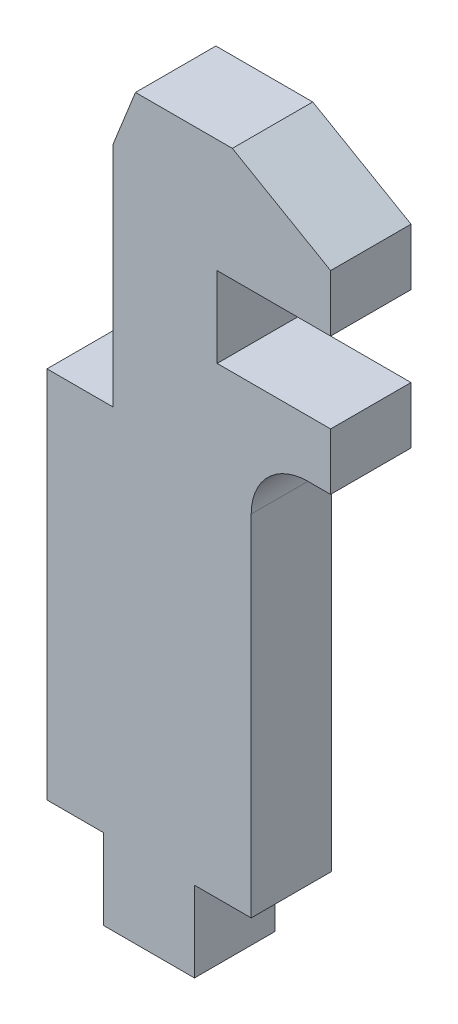
SolidWorks part; units mm, degrees
material "ABS PC"
ref_plane "Front Plane" through (0, 0, 0) normal (0, 0, 1) x (1, 0, 0)
ref_plane "Top Plane" through (0, 0, 0) normal (0, 1, 0) x (1, 0, 0)
ref_plane "Right Plane" through (0, 0, 0) normal (1, 0, 0) x (0, 0, -1)
sketch "Sketch1" plane through (0, 0, 0) normal (0, 0, 1) x (1, 0, 0)
  line L0 (0, 10.45) -> (0, -10.45)
  line L1 (0, -55) -> (0, 55) construction
  line L2 (0, -10.45) -> (3.175, -10.45)
  line L3 (3.175, -10.45) -> (3.175, -14.95)
  line L4 (3.175, -14.95) -> (8.255, -14.95)
  line L5 (8.255, -14.95) -> (8.255, -10.45)
  line L6 (8.255, -10.45) -> (11.43, -10.45)
  line L7 (11.43, -10.45) -> (11.43, 9.125)
  line L8 (15.875, 12.3) -> (15.875, 15.475)
  line L9 (15.875, 15.475) -> (9.525, 15.475)
  line L10 (9.525, 19.975) -> (15.875, 19.975)
  line L11 (9.525, 19.975) -> (9.525, 15.475)
  line L12 (15.875, 19.975) -> (15.875, 23.15)
  line L13 (15.875, 23.15) -> (3.683, 23.15)
  line L14 (3.683, 23.15) -> (3.683, 10.45)
  line L15 (3.683, 10.45) -> (0, 10.45)
  line L16 (15.875, 12.3) -> (14.605, 12.3)
  arc A0 (14.605, 12.3) -> (11.43, 9.125) centre (14.605, 9.125) ccw
  dimension "D10" = 3.175
  dimension "D1" = 4.5
  dimension "D2" = 4.5
  dimension "D3" = 5.08
  dimension "D4" = 3.175
  dimension "D5" = 3.175
  dimension "D6" = 15.875
  dimension "D7" = 3.683
  dimension "D8" = 25.4
  dimension "D9" = 38.1
  dimension "D11" = 3.175
  dimension "D12" = 3.175
  dimension "D13" = 6.35
extrude "Boss-Extrude1" add sketch "Sketch1" along normal mid plane 4.5
sketch "Sketch2" plane through (0, 0, 0) normal (0, 0, 1) x (1, 0, 0)
  line L0 (3.683, 23.15) -> (4.953, 26.325)
  line L1 (4.953, 26.325) -> (10.3757, 26.325)
  line L2 (10.3757, 26.325) -> (15.875, 23.15)
  line L3 (15.875, 23.15) -> (3.683, 23.15) construction
  line L4 (3.683, 23.15) -> (15.875, 23.15)
  dimension "D1" = 3.175
  dimension "D2" = 1.27
  dimension "D3" = 30
extrude "Boss-Extrude2" add sketch "Sketch2" along normal mid plane 4.5
sketch "Sketch3" plane through (0, 10.45, 0) normal (0, 1, 0) x (1, 0, 0)
  line L4 (3.683, 2.25) -> (0, 2.25)
  line L5 (0, 2.25) -> (0, -2.25)
  line L6 (0, -2.25) -> (3.683, -2.25)
  line L7 (3.683, -2.25) -> (3.683, 2.25)
  line L8 (3.683, 2.25) -> (0, 2.25)
  line L9 (0, 2.25) -> (0, -2.25)
  line L10 (0, -2.25) -> (3.683, -2.25)
  line L11 (3.683, -2.25) -> (3.683, 2.25)
  dimension "D1" = 0
extrude "Cut-Extrude1" [suppressed] cut sketch "Sketch3" against normal blind 1.905
sketch "Sketch4" plane through (0, 8.545, 0) normal (0, 1, 0) x (1, 0, 0)
  line L8 (3.683, 2.25) -> (0, 2.25)
  line L9 (0, 2.25) -> (0, -2.25)
  line L10 (0, -2.25) -> (3.683, -2.25)
  line L11 (3.683, -2.25) -> (3.683, 2.25)
extrude "Boss-Extrude3" add sketch "Sketch4" along normal blind 1.143
